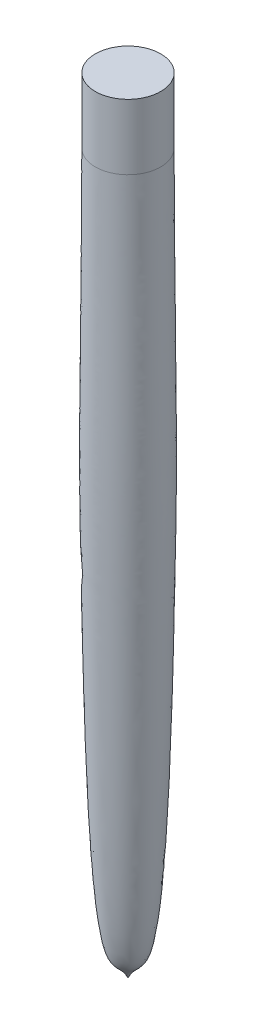
SolidWorks part; units mm, degrees
ref_plane "Front Plane" through (0, 0, 0) normal (0, 0, 1) x (1, 0, 0)
ref_plane "Top Plane" through (0, 0, 0) normal (0, 1, 0) x (1, 0, 0)
ref_plane "Right Plane" through (0, 0, 0) normal (1, 0, 0) x (0, 0, -1)
sketch "Sketch1" plane through (0, 0, 0) normal (0, 0, 1) x (1, 0, 0)
  line L0 (0, 0) -> (0, -152.4)
  line L1 (0, 0) -> (-6.35, 0)
  line L2 (-6.35, 0) -> (-6.35, -12.7)
  spline S0 degree 3 poles (0, -152.4) (-1.1814, -149.8012) (-5.1142, -152.2127) (-7.1808, -54.9913) (-6.5377, -63.026) (-6.35, -12.7) knots 0 0 0 0 0.121076 0.416785 1 1 1 1
  point P6 (-3.9529, -139.975)
  point P8 (-6.1158, -108.2617)
  point P10 (-6.0324, -41.5989)
  point P11 (-5.2754, -102.562)
  point P12 (-5.2754, -99.7218)
  point P13 (-2.4352, -149.2964)
  point P14 (-7.5992, -100.2382)
  point P15 (0, 0)
  point P16 (0, 0)
  point P17 (-6.8246, -44.2086)
  point P18 (-6.5664, -96.3652)
  point P19 (0, 0)
  point P20 (-6.5664, -47.8234)
  point P21 (-6.3082, -93.525)
  dimension "D1" = 152.4
  dimension "D2" = 6.35
  dimension "D3" = 12.7
revolve "Revolve1" add sketch "Sketch1" angle 360 about L0
